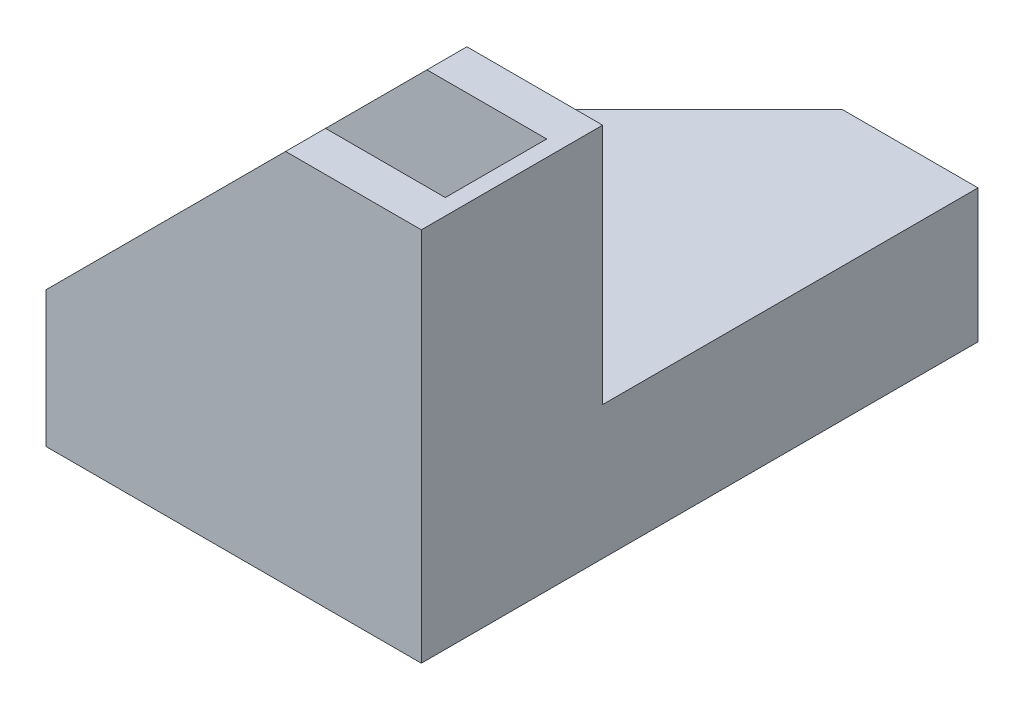
SolidWorks part; units mm, degrees
ref_plane "Front" through (0, 0, 0) normal (0, 0, 1) x (1, 0, 0)
ref_plane "Top" through (0, 0, 0) normal (0, 1, 0) x (1, 0, 0)
ref_plane "Right" through (0, 0, 0) normal (1, 0, 0) x (0, 0, -1)
other "Configuration Table"
sketch "Sketch1" plane through (0, 0, 0) normal (0, 0, 1) x (1, 0, 0)
  line L0 (0, 0) -> (0, 47)
  line L1 (0, 47) -> (-17, 47)
  line L2 (0, 0) -> (-47, 0)
  line L3 (-47, 0) -> (-47, 17)
  line L4 (-17, 47) -> (-47, 17)
extrude "Boss-Extrude1" add sketch "Sketch1" along normal mid plane 22.7
sketch "Sketch2" plane through (0, 0, 0) normal (0, 0, 1) x (1, 0, 0)
  line L0 (-47, 17) -> (-47, 2)
  line L1 (-47, 17) -> (-47, 0) construction
  line L2 (-17, 47) -> (-2, 47)
  line L3 (0, 47) -> (-17, 47) construction
  line L4 (-2, 47) -> (-2, 2)
  line L5 (-2, 2) -> (-47, 2)
  line L6 (-47, 17) -> (-17, 47)
extrude "Cut-Extrude1" cut sketch "Sketch2" against normal mid plane 12.7
sketch "Sketch3" plane through (0, 0, -11.35) normal (0, 0, -1) x (-1, 0, 0)
  line L0 (0, 0) -> (0, 2)
  line L1 (0, 0) -> (0, 47) construction
  line L2 (0, 2) -> (0, 14.7) construction
  line L4 (47, 17) -> (47, 0) construction
  line L5 (47, 2) -> (47, 0)
  line L6 (47, 0) -> (0, 0)
  line L7 (0, 14.7) -> (0, 16.7)
  line L9 (47, 14.7) -> (47, 16.7)
  line L10 (47, 16.7) -> (0, 16.7)
  line L11 (0, 14.7) -> (0, 2)
  line L12 (0, 14.7) -> (2, 14.7) construction
  line L13 (47, 14.7) -> (2, 14.7)
  line L14 (2, 14.7) -> (2, 2)
  line L15 (2, 2) -> (47, 2)
  dimension "D1" = 2
extrude "Boss-Extrude2" add sketch "Sketch3" along normal blind 47
sketch "Sketch4" plane through (0, 16.7, 0) normal (0, 1, 0) x (1, 0, 0)
  line L0 (0, 58.35) -> (-17, 58.35) construction
  line L1 (-47, 58.35) -> (0, 58.35) construction
  line L2 (-47, 11.35) -> (-47, 28.35) construction
  line L3 (-47, 58.35) -> (-47, 11.35) construction
  line L4 (-17, 58.35) -> (-47, 28.35)
  line L5 (-47, 28.35) -> (-47, 58.35)
  line L6 (-47, 58.35) -> (-17, 58.35)
extrude "Cut-Extrude2" cut sketch "Sketch4" against normal blind 47
